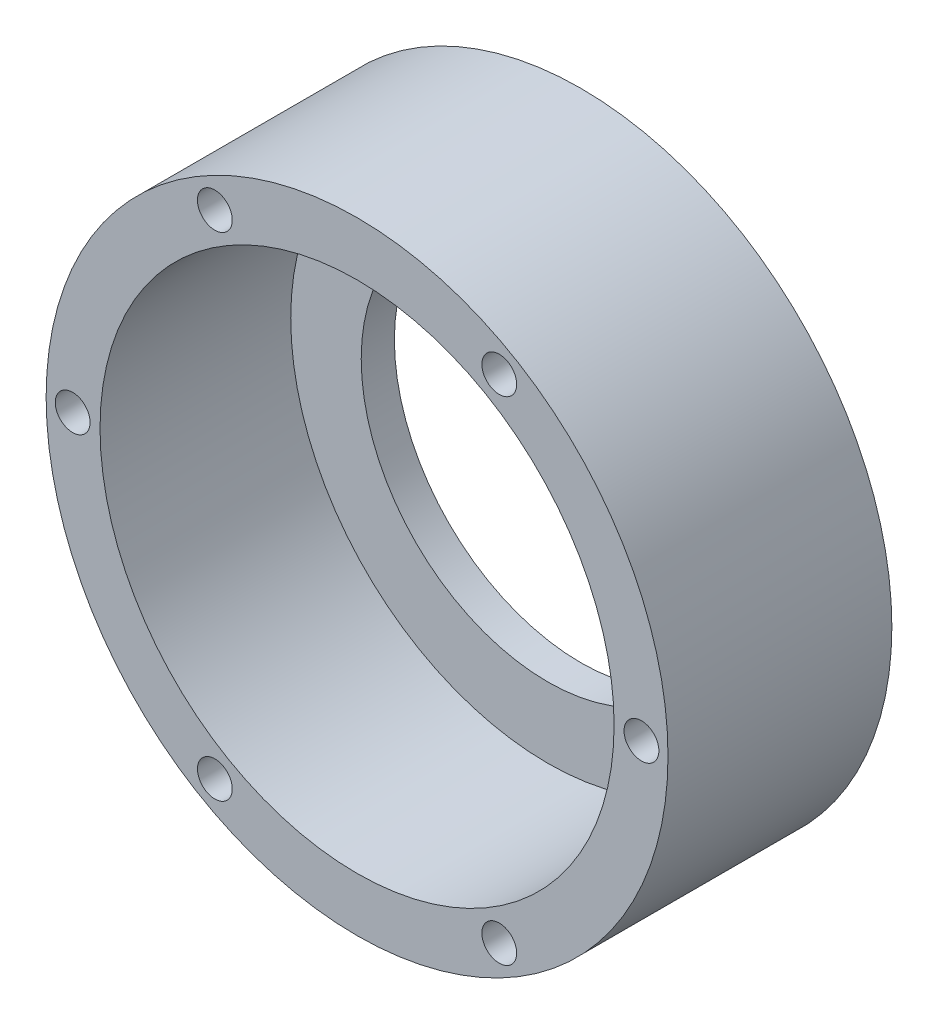
SolidWorks part; units mm, degrees
ref_plane "Alzado" through (0, 0, 0) normal (0, 0, 1) x (1, 0, 0)
ref_plane "Planta" through (0, 0, 0) normal (0, 1, 0) x (1, 0, 0)
ref_plane "Vista lateral" through (0, 0, 0) normal (1, 0, 0) x (0, 0, -1)
sketch "Croquis1" plane through (0, 0, 0) normal (0, 0, 1) x (1, 0, 0)
  circle A0 centre (0, 0) radius 37.5
  dimension "D1" = 75
extrude "Saliente-Extruir1" add sketch "Croquis1" along normal blind 27
sketch "Croquis2" plane through (0, 0, 27) normal (0, 0, 1) x (1, 0, 0)
  circle A0 centre (0, 0) radius 31
  dimension "D1" = 62
extrude "Cortar-Extruir1" cut sketch "Croquis2" against normal blind 23
sketch "Croquis3" plane through (0, 0, 4) normal (0, 0, 1) x (1, 0, 0)
  circle A0 centre (0, 0) radius 22.5
  dimension "D1" = 45
extrude "Cortar-Extruir2" cut sketch "Croquis3" against normal blind 23
sketch "Croquis4" plane through (0, 0, 27) normal (0, 0, 1) x (1, 0, 0)
  line L0 (-34.3, 0) -> (0, 0) construction
  dimension "D1" = 34.3
hole_wizard "Taladro roscado M51" positions "Croquis6" profile "Croquis7" tap size "M5" standard "DIN" end condition through all
sketch "Croquis6" plane through (0, 0, 27) normal (0, 0, 1) x (1, 0, 0)
  point P0 (-34.3, 0)
sketch "Croquis7" plane through (-34.3, 0, 27) normal (1, 0, 0) x (0, -1, 0)
  line L0 (0, 0) -> (0, 27)
  line L1 (0, 27) -> (2.1, 27)
  line L2 (2.1, 27) -> (2.1, 0)
  line L5 (2.1, 0) -> (0, 0)
  line L11 (0, -6.35) -> (0, 107.95) construction
  dimension "Diámetro de perforador para roscar hasta el siguiente" = 4.2
  dimension "Profundidad de perforador para roscar hasta el siguiente" = 27
cosmetic thread "Rosca de taladro1" parameters "D2"=5
pattern_circular "MatrizC1" count 6 over 360 about axis through (0, 0, 0) along (0, 0, 1) of "Taladro roscado M51"
